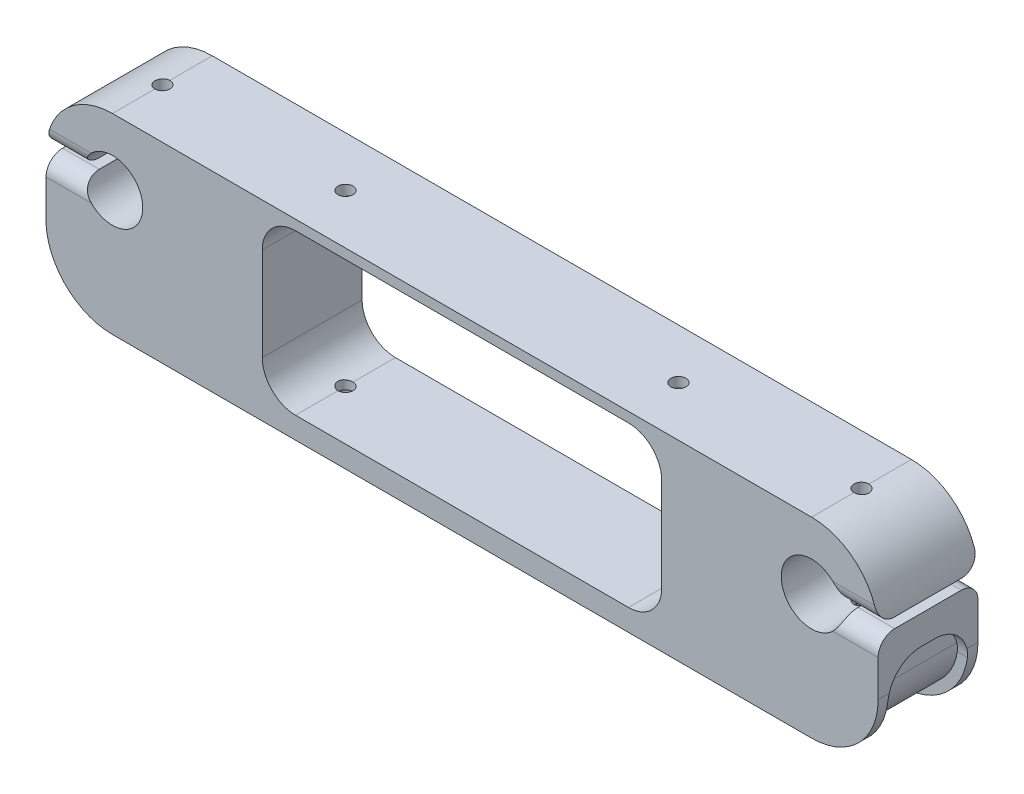
SolidWorks part; units mm, degrees
ref_plane "Front Plane" through (0, 0, 0) normal (0, 0, 1) x (1, 0, 0)
ref_plane "Top Plane" through (0, 0, 0) normal (0, 1, 0) x (1, 0, 0)
ref_plane "Right Plane" through (0, 0, 0) normal (1, 0, 0) x (0, 0, -1)
sketch "Sketch1" plane through (0, 0, 0) normal (0, 0, 1) x (1, 0, 0)
  line L0 (-108.9795, 5.8152) -> (101.0205, 5.8152) construction
  line L1 (100.9111, -31.6848) -> (-108.9795, -31.6848)
  line L2 (76.0205, 5.8152) -> (76.0205, 13.8152) construction
  line L3 (101.0205, 25.8152) -> (-108.9795, 25.8152)
  line L4 (121.0205, 5.8152) -> (121.0205, -11.6851)
  line L5 (-128.9417, -12.9138) -> (-128.9417, 4.5865)
  line L6 (76.0205, 13.8152) -> (-83.9795, 13.8152) construction
  line L7 (-83.9795, 13.8152) -> (-83.9795, 5.8152) construction
  line L8 (-3.9795, 13.8152) -> (-3.9795, 5.8152) construction
  circle A0 centre (-108.9795, 5.8152) radius 9.1
  circle A1 centre (-83.9795, 13.8152) radius 4.125
  arc A2 (-108.9795, 25.8152) -> (-128.9417, 4.5865) centre (-108.9795, 5.8152) ccw
  arc A3 (101.0205, 25.8152) -> (121.0205, 5.8152) centre (101.0205, 5.8152) cw
  circle A4 centre (76.0205, 13.8152) radius 4.125
  circle A5 centre (101.0205, 5.8152) radius 9.1
  arc A6 (121.0205, -11.6851) -> (100.9111, -31.6848) centre (101.0205, -11.6851) cw
  arc A7 (-108.9795, -31.6848) -> (-128.9417, -12.9138) centre (-108.9795, -11.6848) cw
  dimension "D1" = 18.2
  dimension "D3" = 8.25
  dimension "D6" = 37.5
  dimension "D8" = 18.2
  dimension "D9" = 8.25
  dimension "D7" = 20
  dimension "D2" = 160
  dimension "D4" = 8
  dimension "D5" = 210
extrude "Boss-Extrude1" add sketch "Sketch1" along normal blind 30
sketch "Sketch2" plane through (0, 0, 0) normal (0, 0, -1) x (-1, 0, 0)
  line L0 (3.9795, 25.8152) -> (3.9795, -28.1848) construction
  line L1 (-101.0205, 25.8152) -> (108.9795, 25.8152) construction
  line L4 (-46.0205, -25.1848) -> (53.9795, -25.1848)
  line L5 (-56.0205, -15.1848) -> (-56.0205, 12.8152)
  line L6 (-46.0205, 22.8152) -> (53.9795, 22.8152)
  line L7 (63.9795, -15.1848) -> (63.9795, 12.8152)
  line L8 (-56.0205, -25.1848) -> (63.9795, 22.8152) construction
  line L9 (-56.0205, 22.8152) -> (63.9795, -25.1848) construction
  arc A0 (53.9795, 22.8152) -> (63.9795, 12.8152) centre (53.9795, 12.8152) cw
  arc A1 (53.9795, -25.1848) -> (63.9795, -15.1848) centre (53.9795, -15.1848) ccw
  arc A2 (-46.0205, -25.1848) -> (-56.0205, -15.1848) centre (-46.0205, -15.1848) cw
  arc A3 (-56.0205, 12.8152) -> (-46.0205, 22.8152) centre (-46.0205, 12.8152) cw
  point P6 (3.9795, -1.1848)
  dimension "D3" = 10
  dimension "D1" = 3
  dimension "D2" = 120
extrude "Cut-Extrude1" cut sketch "Sketch2" against normal through all both and the other way through all
ref_plane "Plane1" through (0, 0, 15) normal (0, 0, -1) x (-1, 0, 0)
sketch "Sketch3" plane through (0, 0, 15) normal (0, 0, -1) x (-1, 0, 0)
  line L0 (-121.0205, 5.8152) -> (-121.0205, -11.6851)
  line L1 (-121.0205, -4.3133) -> (-121.0205, -11.6851)
  line L2 (-100.9111, -31.6848) -> (108.9795, -31.6848)
  line L3 (-100.9111, -31.6848) -> (-56.0205, -31.6848)
  line L4 (-118.0205, -4.3133) -> (-118.0205, -11.6851)
  line L5 (-100.9197, -28.6848) -> (-56.0205, -28.6848)
  line L6 (-121.0205, -4.3133) -> (-118.0205, -4.3133)
  line L7 (-56.0205, -28.6848) -> (-56.0205, -31.6848)
  line L8 (-56.0205, 12.8152) -> (-56.0205, -15.1848) construction
  line L10 (-100.9197, -28.6848) -> (108.9795, -28.6848) construction
  line L11 (-100.9111, -31.6848) -> (108.9795, -31.6848) construction
  line L12 (-118.0205, 5.8152) -> (-118.0205, -11.6851) construction
  line L13 (-121.0205, 5.8152) -> (-121.0205, -11.6851) construction
  arc A0 (-121.0205, -11.6851) -> (-100.9111, -31.6848) centre (-101.0205, -11.6851) ccw
  arc A1 (-121.0205, -11.6851) -> (-100.9111, -31.6848) centre (-101.0205, -11.6851) ccw
  arc A2 (-118.0205, -11.6851) -> (-100.9197, -28.6848) centre (-101.0205, -11.6851) ccw
  dimension "D1" = 3
extrude "Cut-Extrude2" cut sketch "Sketch3" against normal mid plane 24
fillet "Fillet1" radius 10 4 edges at (119.5205, -4.3133, 3) (119.5205, -4.3133, 27) (56.0205, -30.1848, 3) (56.0205, -30.1848, 27)
ref_plane "Plane2" through (-3.9795, 0, 0) normal (1, 0, 0) x (0, 0, -1)
mirror "Mirror1" about plane through (-3.9795, 0, 0) normal (1, 0, 0) of "Fillet1", "Cut-Extrude2"
sketch "Sketch4" plane through (121.0205, 0, 0) normal (1, 0, 0) x (0, 0, -1)
  line L0 (-30, 5.8152) -> (0, 5.8152)
extrude "Cut-Extrude-Thin1" cut sketch "Sketch4" against normal blind 18 thin thin type mid plane wall 3
fillet "Fillet2" radius 5 4 edges at (115.5083, 4.3152, 0) (115.5083, 4.3152, 30) (115.4801, 7.3152, 30) (115.4801, 7.3152, 0)
sketch "Sketch5" plane through (0, 25.8152, 0) normal (0, 1, 0) x (1, 0, 0)
  line L0 (101.0205, -30) -> (101.0205, 0) construction
  circle A0 centre (101.0205, -15) radius 2.25
  dimension "D1" = 4.5
extrude "Cut-Extrude3" cut sketch "Sketch5" against normal blind 60
sketch "Sketch7" plane through (0, -28.6848, 0) normal (0, -1, 0) x (-1, 0, 0)
  line L1 (-100.9608, -19.3297) -> (-97.241, -17.1131)
  line L2 (-97.241, -17.1131) -> (-97.3008, -12.7834)
  line L3 (-97.3008, -12.7834) -> (-101.0803, -10.6703)
  line L4 (-101.0803, -10.6703) -> (-104.8001, -12.8869)
  line L5 (-104.8001, -12.8869) -> (-104.7403, -17.2166)
  line L6 (-104.7403, -17.2166) -> (-100.9608, -19.3297)
  circle A0 centre (-101.0205, -15) radius 3.75 construction
  dimension "D1" = 7.5
extrude "Cut-Extrude5" cut sketch "Sketch7" against normal blind 23
sketch "Sketch8" plane through (0, 22.8152, 0) normal (0, -1, 0) x (1, 0, 0)
  line L1 (-53.9795, 30) -> (-53.9795, 20) construction
  line L2 (-53.9795, 30) -> (-53.9795, 0) construction
  line L3 (-53.9795, 20) -> (-53.9795, 10) construction
  line L4 (-53.9795, 10) -> (-53.9795, 0) construction
  circle A0 centre (-53.9795, 15) radius 2.25
  dimension "D1" = 4.5
extrude "Cut-Extrude6" cut sketch "Sketch8" against normal blind 23 and the other way blind 77
mirror "Mirror2" about plane through (-3.9795, 0, 0) normal (1, 0, 0) of "Cut-Extrude-Thin1", "Fillet2", "Cut-Extrude3", "Cut-Extrude5", "Cut-Extrude6"
sketch "Sketch9" plane through (0, 0, 30) normal (0, 0, 1) x (1, 0, 0)
  circle A0 centre (-83.9795, 13.8152) radius 6.3658
  circle A1 centre (76.0205, 13.8152) radius 7.3648
extrude "Boss-Extrude2" add sketch "Sketch9" against normal blind 3
sketch "Sketch10" plane through (0, -31.6848, 0) normal (0, -1, 0) x (-1, 0, 0)
  circle A0 centre (-46.0205, -15) radius 3.75
  circle A1 centre (53.9795, -15) radius 3.75
  dimension "D1" = 7.5
  dimension "D2" = 7.5
extrude "Cut-Extrude7" cut sketch "Sketch10" against normal blind 4
